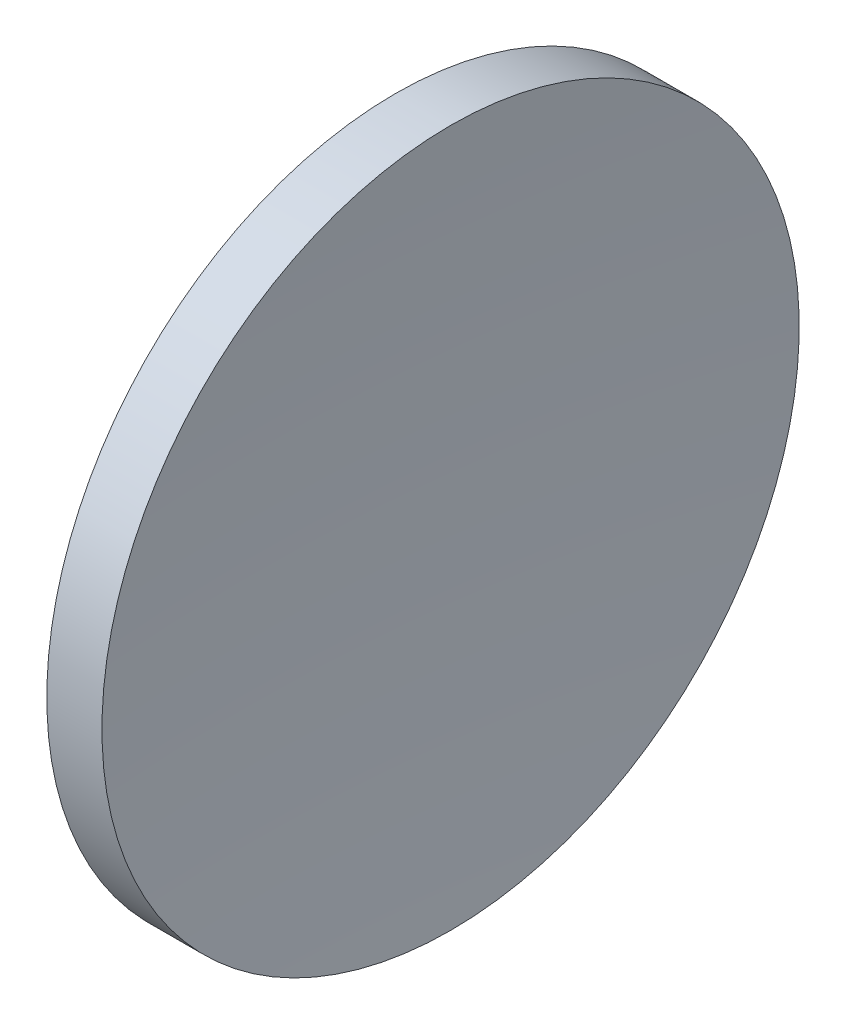
SolidWorks part; units mm, degrees
ref_plane "前视基准面" through (0, 0, 0) normal (0, 0, 1) x (1, 0, 0)
ref_plane "上视基准面" through (0, 0, 0) normal (0, 1, 0) x (1, 0, 0)
ref_plane "右视基准面" through (0, 0, 0) normal (1, 0, 0) x (0, 0, -1)
sketch "草图1" plane through (0, 0, 0) normal (0, 0, 1) x (1, 0, 0)
  line L0 (115.9445, 65.2168) -> (135.9482, 65.2168) construction
  line L1 (124.9126, 84.2418) -> (127.9235, 84.2418)
  line L2 (127.1554, 65.2168) -> (122.8554, 65.2168)
  arc A0 (124.9126, 84.2418) -> (122.8554, 65.2168) centre (211.8554, 65.2168) ccw
  arc A1 (127.9235, 84.2418) -> (127.1554, 65.2168) centre (363.1554, 65.2168) ccw
revolve "旋转1" add sketch "草图1" angle 360 about L0
